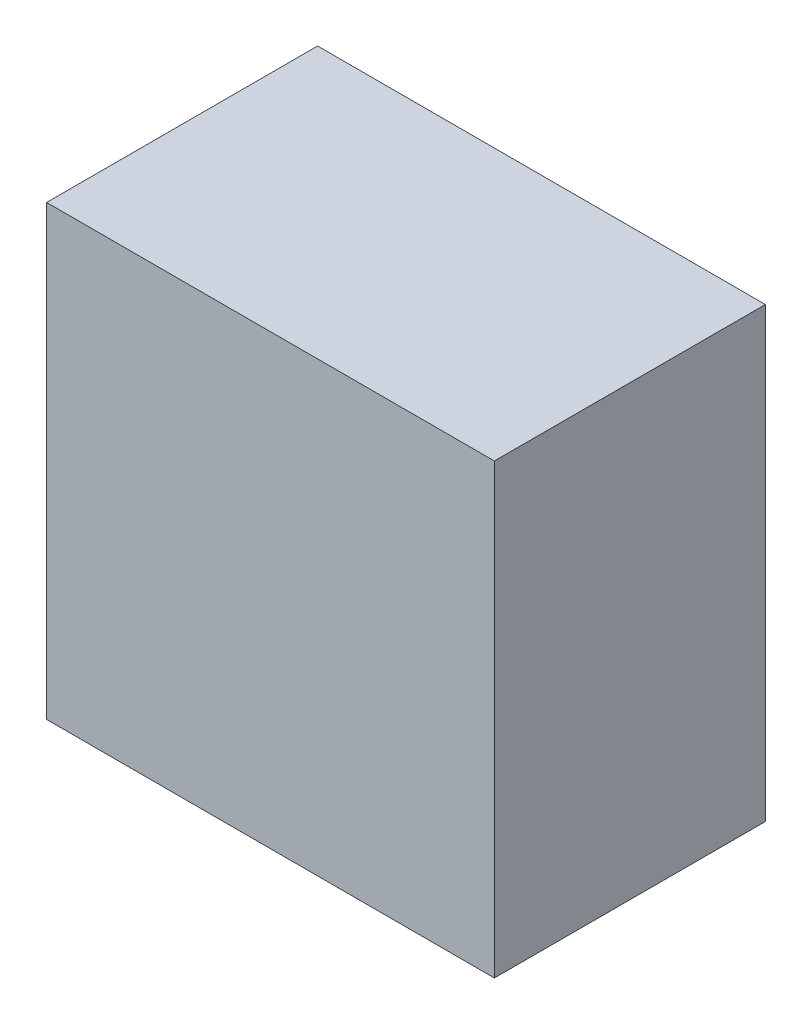
SolidWorks part; units mm, degrees
ref_plane "Plan de face" through (0, 0, 0) normal (0, 0, 1) x (1, 0, 0)
ref_plane "Plan de dessus" through (0, 0, 0) normal (0, 1, 0) x (1, 0, 0)
ref_plane "Plan de droite" through (0, 0, 0) normal (1, 0, 0) x (0, 0, -1)
sketch "Esquisse1" plane through (0, 0, 0) normal (0, 0, 1) x (1, 0, 0)
  line L1 (-170, 170) -> (170, 170)
  line L2 (-170, 170) -> (-170, -170)
  line L3 (-170, -170) -> (170, -170)
  line L4 (170, 170) -> (170, -170)
  line L5 (-170, 170) -> (170, -170) construction
  line L6 (-170, -170) -> (170, 170) construction
  line L7 (-190, 190) -> (190, 190)
  line L8 (-190, 190) -> (-190, -190)
  line L9 (-190, -190) -> (190, -190)
  line L10 (190, 190) -> (190, -190)
  line L11 (-190, 190) -> (190, -190) construction
  line L12 (-190, -190) -> (190, 190) construction
  point P0 (0, 0)
  point P6 (0, 0)
  dimension "D1" = 340
  dimension "D2" = 340
  dimension "D3" = 380
  dimension "D4" = 380
extrude "Boss.-Extru.1" add sketch "Esquisse1" along normal blind 210
sketch "Esquisse2" plane through (0, 0, 210) normal (0, 0, 1) x (1, 0, 0)
  line L1 (-190, 190) -> (190, 190)
  line L2 (-190, 190) -> (-190, -190)
  line L3 (-190, -190) -> (190, -190)
  line L4 (190, 190) -> (190, -190)
  line L5 (-190, 190) -> (190, -190) construction
  line L6 (-190, -190) -> (190, 190) construction
  point P0 (0, 0)
extrude "Boss.-Extru.2" add sketch "Esquisse2" along normal blind 20
